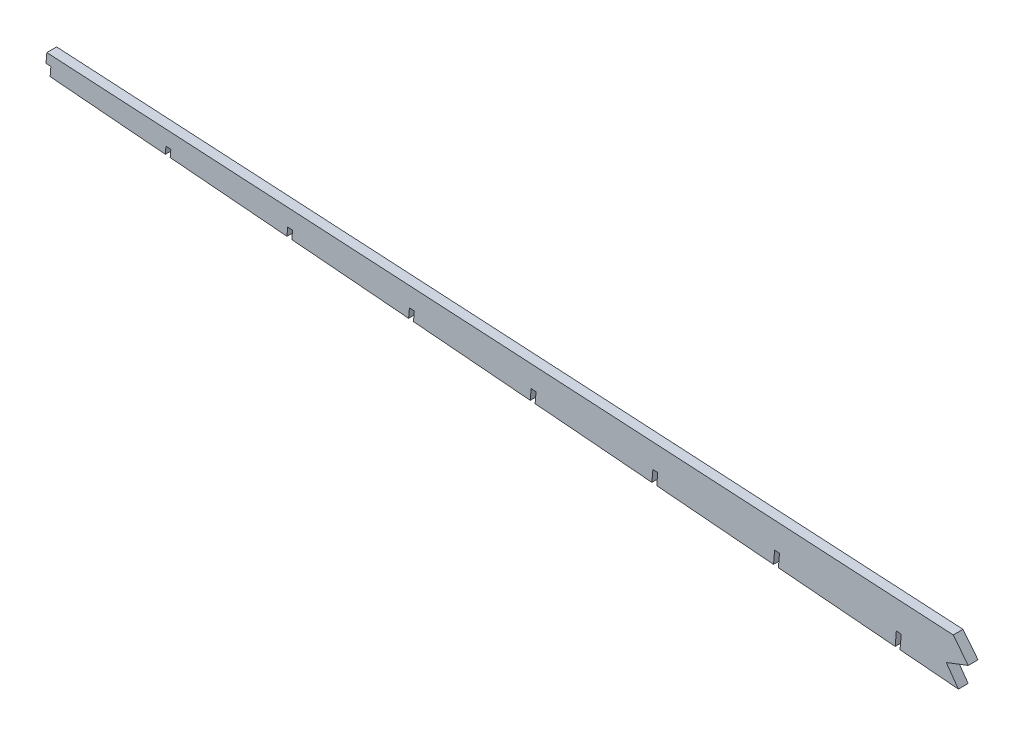
SolidWorks part; units mm, degrees
material "Balsa"
ref_plane "Front Plane" through (0, 0, 0) normal (0, 0, 1) x (1, 0, 0)
ref_plane "Top Plane" through (0, 0, 0) normal (0, 1, 0) x (1, 0, 0)
ref_plane "Right Plane" through (0, 0, 0) normal (1, 0, 0) x (0, 0, -1)
sketch "Sketch1" plane through (0, 0, 0) normal (0, 0, 1) x (1, 0, 0)
  line L0 (76.2, 56.7475) -> (76.2, 37.6975)
  line L1 (79.375, 56.7475) -> (79.375, 37.6975)
  line L2 (0, 44.0475) -> (0, 31.3475)
  line L3 (3.175, 44.0475) -> (3.175, 31.3475)
  line L4 (-5.7133, 44.4467) -> (-6.776, 31.7912)
  line L5 (-2.5494, 44.181) -> (-3.6121, 31.5255)
  line L6 (-1.4923, 31.3475) -> (25.4, 31.3475)
  line L7 (25.4, 31.3475) -> (69.85, 37.6975)
  line L8 (-2.5494, 44.181) -> (-0.424, 69.4919) construction
  line L9 (-0.424, 69.4919) -> (-3.5879, 69.7576)
  line L10 (-3.5879, 69.7576) -> (-5.7133, 44.4467) construction
  line L11 (-5.7133, 44.4467) -> (-2.5494, 44.181)
  line L12 (3.175, 44.0475) -> (3.175, 69.4475) construction
  line L13 (3.175, 69.4475) -> (0, 69.4475)
  line L14 (0, 69.4475) -> (0, 44.0475) construction
  line L15 (0, 44.0475) -> (3.175, 44.0475)
  line L16 (92.075, 37.6975) -> (92.075, 46.5875)
  line L17 (-942.8808, 122.7744) -> (-947.5199, 67.5279)
  line L18 (0, 69.4475) -> (-0.424, 69.4919)
  line L19 (3.175, 69.4475) -> (152.4, 69.4475)
  line L20 (152.4, 69.4475) -> (152.4, 37.6975)
  line L21 (152.4, 37.6975) -> (69.85, 37.6975)
  line L22 (92.075, 46.5875) -> (95.25, 46.5875)
  line L23 (95.25, 46.5875) -> (95.25, 37.6975)
  line L24 (-1.4923, 31.3475) -> (-943.9128, 110.4848)
  line L25 (79.375, 69.4475) -> (79.375, 56.7475)
  line L26 (-942.8808, 122.7744) -> (-3.5879, 69.7576)
  line L27 (136.525, 37.6975) -> (136.525, 46.5875)
  line L28 (76.2, 69.4475) -> (76.2, 56.7475)
  line L29 (79.375, 56.7475) -> (76.2, 56.7475)
  line L30 (-943.5688, 114.5813) -> (-5.7133, 44.4467)
  line L31 (136.525, 46.5875) -> (139.7, 46.5875)
  line L32 (139.7, 46.5875) -> (139.7, 37.6975)
  line L33 (15.875, 31.3475) -> (15.875, 36.4275)
  line L34 (15.875, 36.4275) -> (19.05, 36.4275)
  line L35 (19.05, 36.4275) -> (19.05, 31.3475)
  line L36 (-942.8808, 122.7744) -> (-946.0519, 122.9534)
  line L37 (-946.0519, 122.9534) -> (-946.5835, 116.6233)
  line L38 (-946.5835, 116.6233) -> (-943.4123, 116.4443)
  dimension "D3" = 76.2
  dimension "D10" = 12.3329
  dimension "D11" = 8.2219
  dimension "D2" = 25.4
  dimension "D4" = 25.4
  dimension "D5" = 12.7
  dimension "D7" = 3.175
  dimension "D9" = 3.175
  dimension "D12" = 3.175
  dimension "D6" = 19.05
  dimension "D13" = 6.35
  dimension "D14" = 12.7
  dimension "D16" = 3.175
  dimension "D17" = 3.175
  dimension "D18" = 12.7
  dimension "D19" = 12.7
  dimension "D20" = 8.89
  dimension "D21" = 8.89
  dimension "D15" = 76.2
  dimension "D22" = 12.7
  dimension "D23" = 3.175
  dimension "D24" = 5.08
  dimension "D8" = 6.35
  dimension "D25" = 3.175
  dimension "D26" = 6.35
extrude "Boss-Extrude1" add sketch "Sketch1" along normal mid plane 6.35 contours L17 L30 L11 L5 L24 L6 L2 L15 L3 L7 L21 L0 L28 L19 L13 L18 L9 L26 | L30 L17 L24 L4 | L29 L25 L19 L28 | L19 L25 L1 L21 L20 | L37 L38 L17 L36
sketch "Sketch2" plane through (0, 0, 3.175) normal (0, 0, 1) x (1, 0, 0)
  line L2 (-73.2652, 73.2231) -> (-80.3969, -11.7061)
  line L3 (-943.5688, 114.5813) -> (-5.7133, 44.4467)
  line L6 (-76.4291, 73.4888) -> (-83.5608, -11.4404)
  line L7 (-6.776, 31.7912) -> (-943.9128, 110.4848)
  line L10 (-152.4177, 77.6821) -> (-159.3225, -4.5442)
  line L14 (-155.5816, 77.9478) -> (-162.4863, -4.2785)
  line L18 (-231.5658, 82.1932) -> (-238.251, 2.5812)
  line L22 (-234.7297, 82.4589) -> (-241.4149, 2.8469)
  line L26 (-310.7178, 86.6582) -> (-317.1769, 9.7387)
  line L30 (-313.8817, 86.9239) -> (-320.3408, 10.0043)
  line L34 (-389.8657, 91.1713) -> (-396.1056, 16.8623)
  line L38 (-393.0296, 91.437) -> (-399.2695, 17.128)
  line L42 (-469.0186, 95.6263) -> (-475.031, 24.0265)
  line L46 (-472.1824, 95.892) -> (-478.1948, 24.2921)
  line L50 (-548.1666, 100.1381) -> (-553.9596, 31.1506)
  line L54 (-551.3305, 100.4038) -> (-557.1235, 31.4163)
  line L58 (-627.3195, 104.5918) -> (-632.8849, 38.3152)
  line L62 (-630.4834, 104.8575) -> (-636.0488, 38.5809)
  line L66 (-706.4673, 109.1069) -> (-711.8138, 45.4365)
  line L70 (-709.6312, 109.3725) -> (-714.9777, 45.7022)
  line L74 (-785.6206, 113.5558) -> (-790.7389, 52.6041)
  line L78 (-788.7845, 113.8214) -> (-793.9027, 52.8697)
  line L82 (-864.7684, 118.071) -> (-869.6679, 59.7246)
  line L86 (-867.9323, 118.3366) -> (-872.8317, 59.9902)
  line L89 (-942.9091, 122.4365) -> (-947.5795, 66.8182)
  line M2 (-943.9128, 110.4848) -> (-6.776, 31.7912)
extrude "Cut-Extrude1" cut sketch "Sketch2" against normal through all contours L3 L6 L2 M2 | L3 L14 L7 L10 | L3 L22 L7 L18 | L3 L30 L7 L26 | L3 L38 L7 L34 | L3 L46 L7 L42 | L3 L54 L7 L50 | L3 L62 L7 L58 | L3 L70 L7 L66 | L3 L78 L7 L74 | L3 L86 L7 L82
sketch "Sketch3" plane through (0, 0, 3.175) normal (0, 0, 1) x (1, 0, 0)
  line L0 (-354.2316, 60.9679) -> (-362.1267, 71.9794)
  line L1 (-316.3285, 57.7851) -> (-392.1347, 64.1507) construction
  line L2 (-362.1267, 71.9794) -> (-347.8724, 77.4491)
  line L3 (-347.8724, 77.4491) -> (-357.599, 89.7392)
  line L4 (-946.0519, 122.9534) -> (-3.5879, 69.7576) construction
  line L5 (-357.599, 89.7392) -> (194.2184, 89.7392)
  line L6 (194.2184, 89.7392) -> (127.8118, -85.756)
  line L7 (127.8118, -85.756) -> (-354.2316, 60.9679)
extrude "Cut-Extrude2" cut sketch "Sketch3" against normal blind 7.62 contours L7 L0 L2 L3 L5 L6
equation "\"D11@Sketch1\"=\"D10@Sketch1\"*(2/3)"
